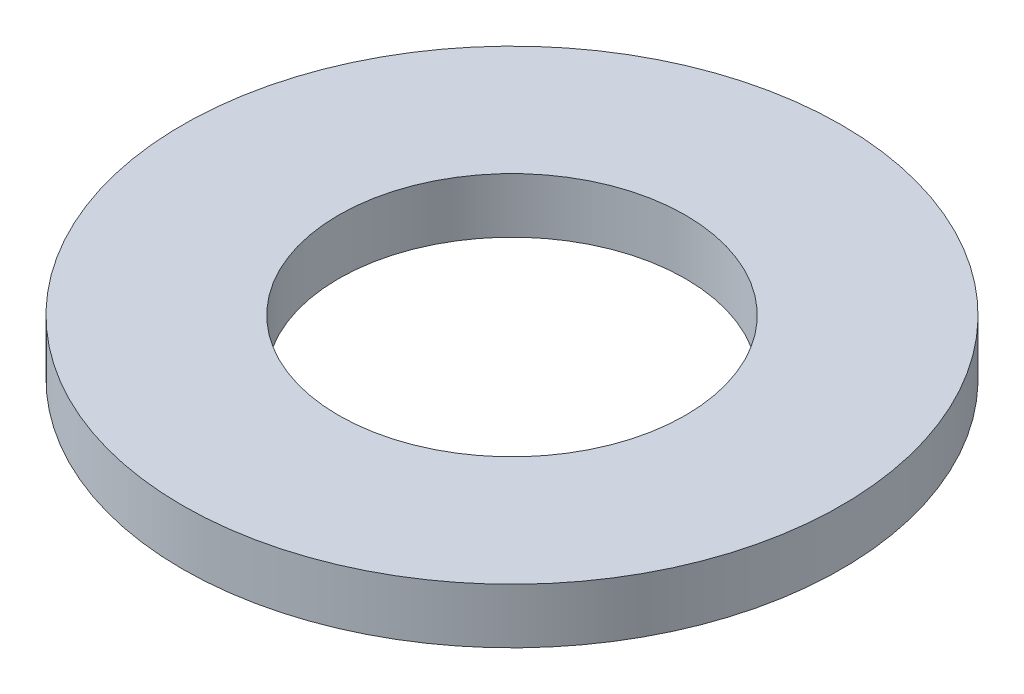
SolidWorks part; units mm, degrees
ref_plane "Front Plane" through (0, 0, 0) normal (0, 0, 1) x (1, 0, 0)
ref_plane "Top Plane" through (0, 0, 0) normal (0, 1, 0) x (1, 0, 0)
ref_plane "Right Plane" through (0, 0, 0) normal (1, 0, 0) x (0, 0, -1)
sketch "Sketch1" plane through (0, 0, 0) normal (0, 1, 0) x (1, 0, 0)
  circle A0 centre (0, 0) radius 38
  circle A1 centre (0, 0) radius 20
  dimension "D1" = 76
  dimension "D2" = 40
extrude "Boss-Extrude1" add sketch "Sketch1" along normal blind 6.35
